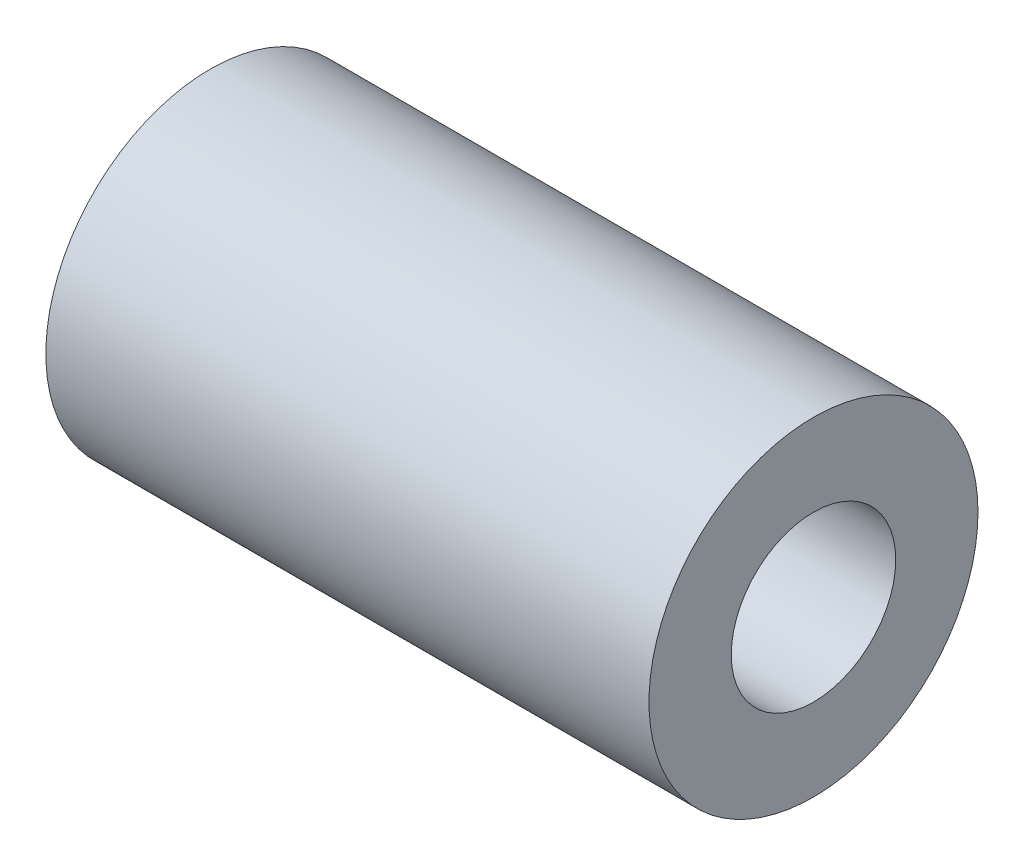
SolidWorks part; units mm, degrees
material "Nylon 101"
ref_plane "Front Plane" through (0, 0, 0) normal (0, 0, 1) x (1, 0, 0)
ref_plane "Top Plane" through (0, 0, 0) normal (0, 1, 0) x (1, 0, 0)
ref_plane "Right Plane" through (0, 0, 0) normal (1, 0, 0) x (0, 0, -1)
sketch "Sketch1" plane through (0, 0, 0) normal (1, 0, 0) x (0, 0, -1)
  circle A0 centre (0, 0) radius 9.525
  circle A1 centre (0, 0) radius 4.7625
  dimension "D1" = 9.525
  dimension "D2" = 19.05
extrude "Boss-Extrude1" add sketch "Sketch1" along normal blind 34.925
